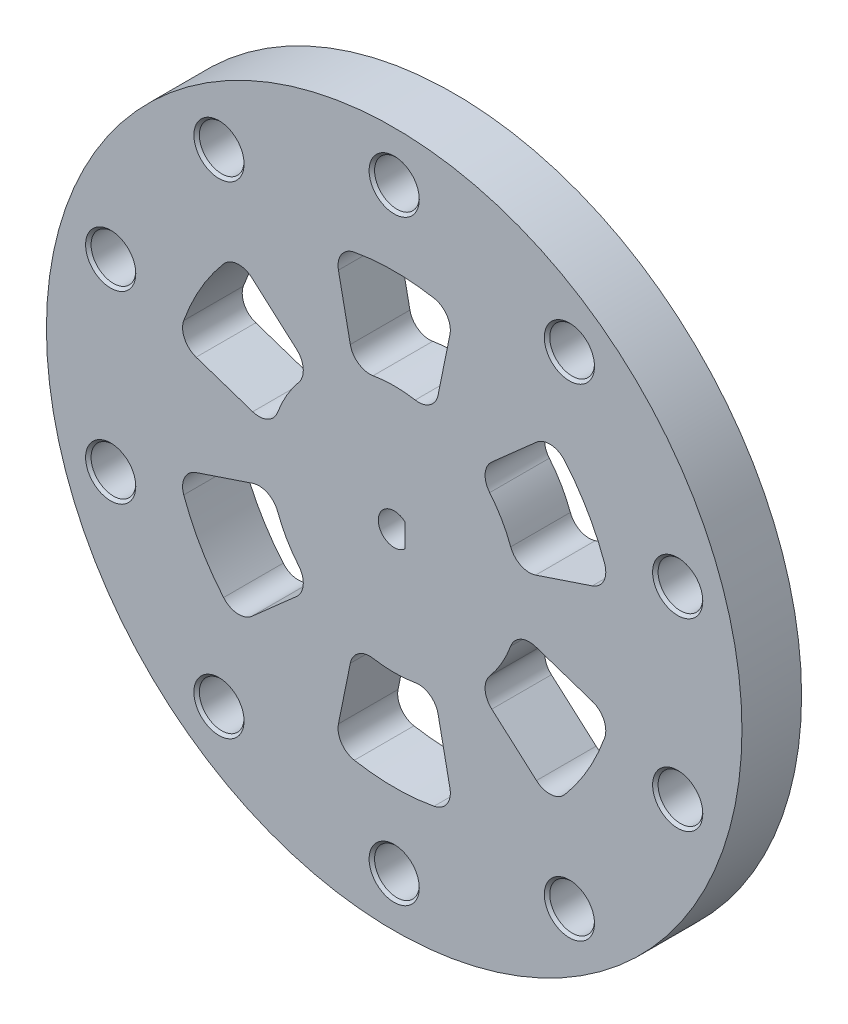
SolidWorks part; units mm, degrees
material "ABS"
ref_plane "Front Plane" through (0, 0, 0) normal (0, 0, 1) x (1, 0, 0)
ref_plane "Top Plane" through (0, 0, 0) normal (0, 1, 0) x (1, 0, 0)
ref_plane "Right Plane" through (0, 0, 0) normal (1, 0, 0) x (0, 0, -1)
sketch "Sketch1" plane through (0, 0, 0) normal (0, 0, 1) x (1, 0, 0)
  line L0 (-4, 11.8427) -> (-6, 21.6852)
  line L1 (4, 11.8427) -> (6, 21.6852)
  line L2 (0, 5.3196) -> (0, -5.2865) construction
  line L3 (12.2561, 2.4573) -> (21.78, 5.6465)
  line L4 (8.2561, 9.3855) -> (15.78, 16.0388)
  line L5 (8.2561, -9.3855) -> (15.78, -16.0388)
  line L6 (12.2561, -2.4573) -> (21.78, -5.6465)
  line L7 (-4, -11.8427) -> (-6, -21.6852)
  line L8 (4, -11.8427) -> (6, -21.6852)
  line L9 (-12.2561, -2.4573) -> (-21.78, -5.6465)
  line L10 (-8.2561, -9.3855) -> (-15.78, -16.0388)
  line L11 (-8.2561, 9.3855) -> (-15.78, 16.0388)
  line L12 (-12.2561, 2.4573) -> (-21.78, 5.6465)
  circle A0 centre (0, 0) radius 12.5
  circle A1 centre (0, 0) radius 35
  circle A2 centre (0, 0) radius 22.5 construction
  arc A3 (-6, 21.6852) -> (6, 21.6852) centre (0, 0) cw
  arc A4 (15.78, 16.0388) -> (21.78, 5.6465) centre (0, 0) cw
  arc A5 (21.78, -5.6465) -> (15.78, -16.0388) centre (0, 0) cw
  arc A6 (6, -21.6852) -> (-6, -21.6852) centre (0, 0) cw
  arc A7 (-15.78, -16.0388) -> (-21.78, -5.6465) centre (0, 0) cw
  arc A8 (-21.78, 5.6465) -> (-15.78, 16.0388) centre (0, 0) cw
  point P34 (0, 0)
  dimension "D1" = 70
  dimension "D2" = 25
  dimension "D3" = 45
  dimension "D4" = 12
  dimension "D5" = 8
  dimension "D6" = 6
extrude "Boss-Extrude2" add sketch "Sketch1" along normal mid plane 6 contours A0 | A1 L12 A8 L11 A0 L0 A3 L1 L4 A4 L3 L6 A5 L5 L8 A6 L7 L10 A7 L9
fillet "Fillet1" radius 2 24 edges at (4, 11.8427, 0) (-4, 11.8427, 0) (6, 21.6852, 0) (-6, 21.6852, 0) (-15.78, -16.0388, 0) (-12.2561, 2.4573, 0) (12.2561, 2.4573, 0) (15.78, -16.0388, 0) (21.78, -5.6465, 0) (4, -11.8427, 0) (-12.2561, -2.4573, 0) (-4, -11.8427, 0) (12.2561, -2.4573, 0) (-15.78, 16.0388, 0) (15.78, 16.0388, 0) (-8.2561, 9.3855, 0) (-8.2561, -9.3855, 0) (6, -21.6852, 0) (21.78, 5.6465, 0) (-6, -21.6852, 0) (-21.78, 5.6465, 0) (-21.78, -5.6465, 0) (8.2561, -9.3855, 0) (8.2561, 9.3855, 0)
sketch "Sketch4" plane through (0, 0, -3) normal (0, 0, -1) x (-1, 0, 0)
  line L1 (-1.1, 1.1619) -> (-1.1, -1.1619)
  arc A1 (-1.1, -1.1619) -> (-1.1, 1.1619) centre (0, 0) ccw
extrude "Cut-Extrude1" cut sketch "Sketch4" against normal through all both
hole_wizard "Ø5.0mm Dowel Hole1" positions "Sketch5" profile "Sketch6" hole size "Ø5.0" standard "ANSI Metric"
sketch "Sketch5" plane through (0, 0, 3) normal (0, 0, 1) x (1, 0, 0)
  point P0 (0, 30)
  dimension "D1" = 30
sketch "Sketch6" plane through (0, 30, 3) normal (1, 0, 0) x (0, -1, 0)
  line L0 (0, 0) -> (0, 21.3519)
  line L1 (0, 21.3519) -> (2.25, 20)
  line L2 (2.25, 20) -> (2.25, 0.275)
  line L3 (2.25, 0.275) -> (2.525, 0)
  line L5 (2.525, 0) -> (0, 0)
  line L6 (-2.25, 0.275) -> (-2.525, 0) construction
  line L10 (0, 21.3519) -> (-2.25, 20) construction
  line L11 (0, -6.35) -> (0, 107.95) construction
  dimension "Hole Dia." = 4.5
  dimension "Hole Depth" = 20
  dimension "Near C'Sink Dia." = 5.05
  dimension "Near C'Sink Angle" = 90
  dimension "Drill Angle" = 118
pattern_circular "CirPattern4" count 10 over 360 about axis through (0, 0, 0) along (0, 0, 1) of "Ø5.0mm Dowel Hole1"
